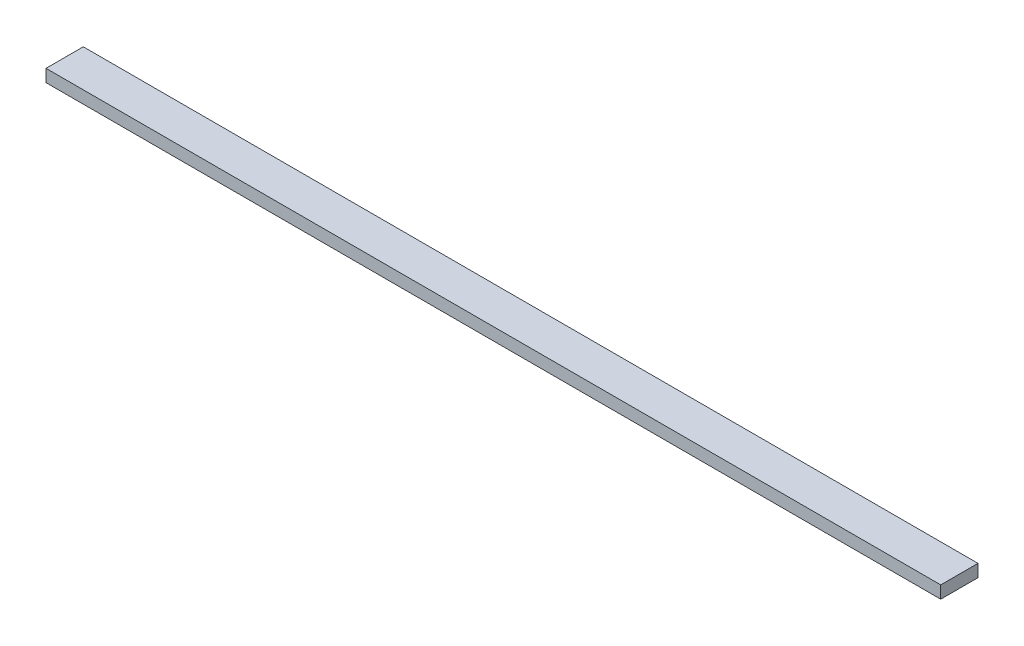
SolidWorks part; units mm, degrees
ref_plane "Front Plane" through (0, 0, 0) normal (0, 0, 1) x (1, 0, 0)
ref_plane "Top Plane" through (0, 0, 0) normal (0, 1, 0) x (1, 0, 0)
ref_plane "Right Plane" through (0, 0, 0) normal (1, 0, 0) x (0, 0, -1)
sketch "Sketch1" plane through (0, 0, 0) normal (0, 1, 0) x (1, 0, 0)
  line L1 (0, 0) -> (914.4, 0)
  line L2 (0, 0) -> (0, 38.1)
  line L3 (0, 38.1) -> (914.4, 38.1)
  line L4 (914.4, 0) -> (914.4, 38.1)
  dimension "D1" = 914.4
  dimension "D2" = 38.1
extrude "Boss-Extrude1" add sketch "Sketch1" along normal blind 12.7
